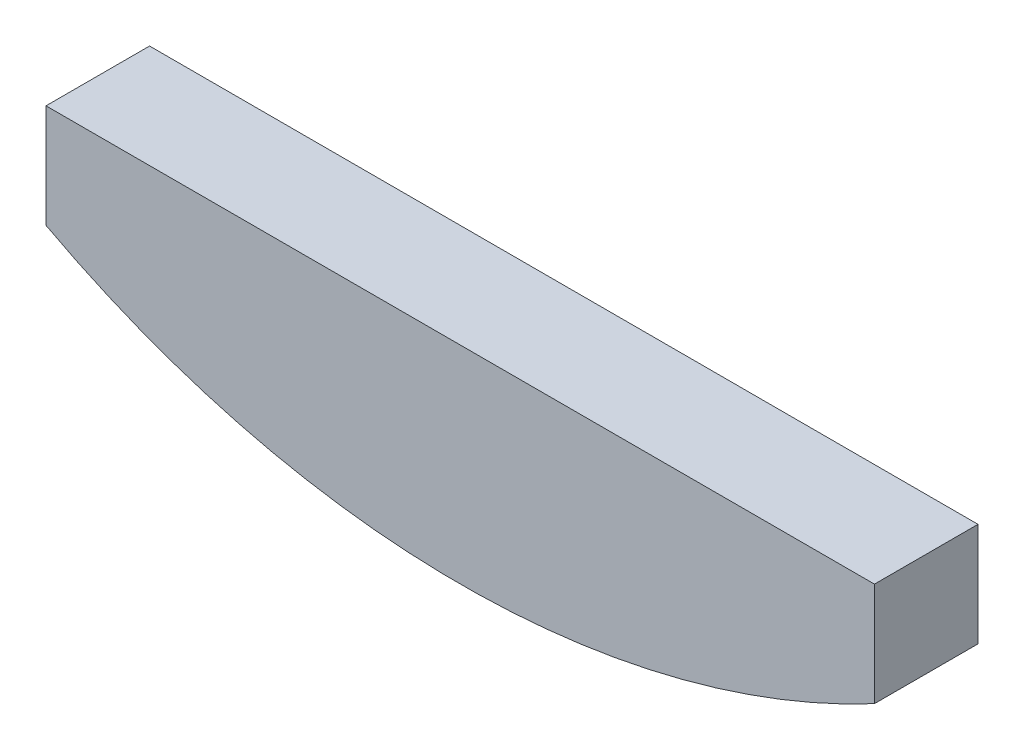
SolidWorks part; units mm, degrees
ref_plane "Front Plane" through (0, 0, 0) normal (0, 0, 1) x (1, 0, 0)
ref_plane "Top Plane" through (0, 0, 0) normal (0, 1, 0) x (1, 0, 0)
ref_plane "Right Plane" through (0, 0, 0) normal (1, 0, 0) x (0, 0, -1)
sketch "Sketch1" plane through (0, 0, 0) normal (0, 0, 1) x (1, 0, 0)
  line L2 (0, 0) -> (0, 6.35)
  line L3 (0, 6.35) -> (50.8, 6.35)
  line L4 (50.8, 0) -> (50.8, 6.35)
  arc A0 (0, 0) -> (50.8, 0) centre (25.4, 47.625) ccw
  dimension "D3" = 50.8
  dimension "D4" = 53.975
  dimension "D1" = 50.8
  dimension "D2" = 6.35
extrude "Boss-Extrude1" add sketch "Sketch1" along normal blind 6.35
